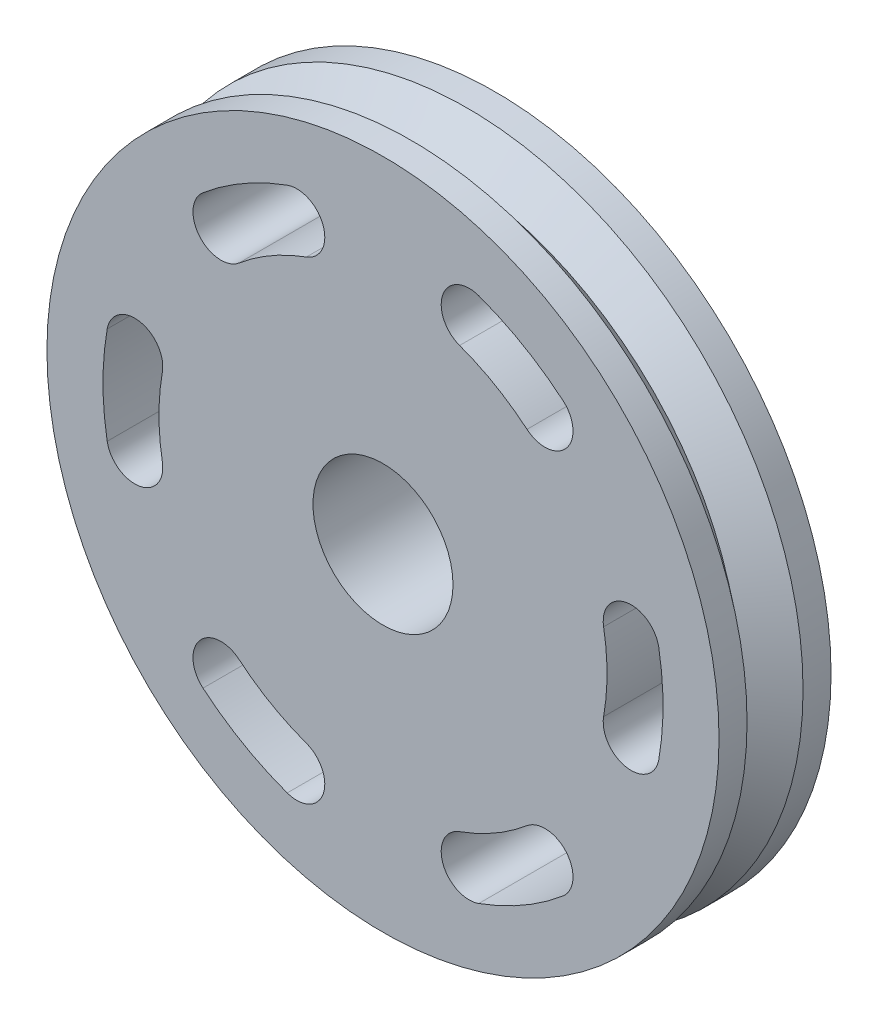
SolidWorks part; units mm, degrees
material "2018 Alloy"
ref_plane "Front Plane" through (0, 0, 0) normal (0, 0, 1) x (1, 0, 0)
ref_plane "Top Plane" through (0, 0, 0) normal (0, 1, 0) x (1, 0, 0)
ref_plane "Right Plane" through (0, 0, 0) normal (1, 0, 0) x (0, 0, -1)
sketch "Sketch1" plane through (0, 0, 0) normal (1, 0, 0) x (0, 0, -1)
  line L0 (0, 2.308) -> (0, -2.092) construction
  line L2 (0, 2.69) -> (-0.25, 3)
  line L3 (-0.25, 3) -> (-0.5, 3)
  line L4 (-0.5, 3) -> (-0.5, 0)
  line L5 (-0.5, 0) -> (0.5, 0)
  line L6 (-0.25, 3) -> (-0.25, 0)
  line L7 (0, 2.69) -> (0.25, 3)
  line L8 (0.25, 3) -> (0.25, 0)
  line L9 (0.25, 3) -> (0.5, 3)
  line L10 (0.5, 3) -> (0.5, 0)
  line L11 (-1.4045, 0) -> (1.604, 0) construction
  dimension "D1" = 0.25
  dimension "D2" = 1
  dimension "D3" = 0.31
  dimension "D4" = 3
revolve "Revolve2" add sketch "Sketch1" angle 360 about L11
sketch "Sketch2" plane through (0, 0, 0.5) normal (0, 0, 1) x (1, 0, 0)
  line L0 (0, 3) -> (0, -3) construction
  line L1 (-3, 0) -> (3, 0) construction
  line L2 (0, 0) -> (-2.2158, 0.3907) construction
  line L3 (0, 0) -> (-2.2158, -0.3907) construction
  circle A0 centre (0, 0) radius 3 construction
  circle A1 centre (0, 0) radius 2.25 construction
  arc A2 (-2.2158, 0.3907) -> (-2.2158, -0.3907) centre (0, 0) ccw construction
  arc A3 (-2.462, 0.4341) -> (-2.462, -0.4341) centre (0, 0) ccw
  arc A4 (-1.9696, 0.3473) -> (-1.9696, -0.3473) centre (0, 0) ccw
  arc A5 (-1.9696, 0.3473) -> (-2.462, 0.4341) centre (-2.2158, 0.3907) ccw
  arc A6 (-2.462, -0.4341) -> (-1.9696, -0.3473) centre (-2.2158, -0.3907) ccw
  arc A7 (-0.684, 1.8794) -> (-1.2856, 1.5321) centre (0, 0) ccw
  arc A8 (-0.684, 1.8794) -> (-0.8551, 2.3492) centre (-0.7695, 2.1143) ccw
  arc A9 (-1.607, 1.9151) -> (-1.2856, 1.5321) centre (-1.4463, 1.7236) ccw
  arc A10 (-0.8551, 2.3492) -> (-1.607, 1.9151) centre (0, 0) ccw
  arc A11 (-0.7695, 2.1143) -> (-1.4463, 1.7236) centre (0, 0) ccw construction
  arc A12 (1.2856, 1.5321) -> (0.684, 1.8794) centre (0, 0) ccw
  arc A13 (1.2856, 1.5321) -> (1.607, 1.9151) centre (1.4463, 1.7236) ccw
  arc A14 (0.8551, 2.3492) -> (0.684, 1.8794) centre (0.7695, 2.1143) ccw
  arc A15 (1.607, 1.9151) -> (0.8551, 2.3492) centre (0, 0) ccw
  arc A16 (1.4463, 1.7236) -> (0.7695, 2.1143) centre (0, 0) ccw construction
  arc A17 (1.9696, -0.3473) -> (1.9696, 0.3473) centre (0, 0) ccw
  arc A18 (1.9696, -0.3473) -> (2.462, -0.4341) centre (2.2158, -0.3907) ccw
  arc A19 (2.462, 0.4341) -> (1.9696, 0.3473) centre (2.2158, 0.3907) ccw
  arc A20 (2.462, -0.4341) -> (2.462, 0.4341) centre (0, 0) ccw
  arc A21 (2.2158, -0.3907) -> (2.2158, 0.3907) centre (0, 0) ccw construction
  arc A22 (0.684, -1.8794) -> (1.2856, -1.5321) centre (0, 0) ccw
  arc A23 (0.684, -1.8794) -> (0.8551, -2.3492) centre (0.7695, -2.1143) ccw
  arc A24 (1.607, -1.9151) -> (1.2856, -1.5321) centre (1.4463, -1.7236) ccw
  arc A25 (0.8551, -2.3492) -> (1.607, -1.9151) centre (0, 0) ccw
  arc A26 (0.7695, -2.1143) -> (1.4463, -1.7236) centre (0, 0) ccw construction
  arc A27 (-1.2856, -1.5321) -> (-0.684, -1.8794) centre (0, 0) ccw
  arc A28 (-1.2856, -1.5321) -> (-1.607, -1.9151) centre (-1.4463, -1.7236) ccw
  arc A29 (-0.8551, -2.3492) -> (-0.684, -1.8794) centre (-0.7695, -2.1143) ccw
  arc A30 (-1.607, -1.9151) -> (-0.8551, -2.3492) centre (0, 0) ccw
  arc A31 (-1.4463, -1.7236) -> (-0.7695, -2.1143) centre (0, 0) ccw construction
  circle A32 centre (0, 0) radius 0.625
  point P10 (-2.25, 0)
  point P21 (-1.125, 1.9486)
  point P28 (1.125, 1.9486)
  point P35 (2.25, 0)
  point P42 (1.125, -1.9486)
  point P49 (-1.125, -1.9486)
  point P56 (0, 0)
  dimension "D1" = 4.5
  dimension "D4" = 0.25
  dimension "D6" = 1.25
  dimension "D2" = 10
  dimension "D3" = 20
  dimension "D5" = 6
extrude "Cut-Extrude1" cut sketch "Sketch2" against normal through all contours A10 A9 A7 A8 | A4 A5 A3 A6 | A30 A29 A27 A28 | A25 A24 A22 A23 | A20 A19 A17 A18 | A32 | A15 A14 A12 A13
